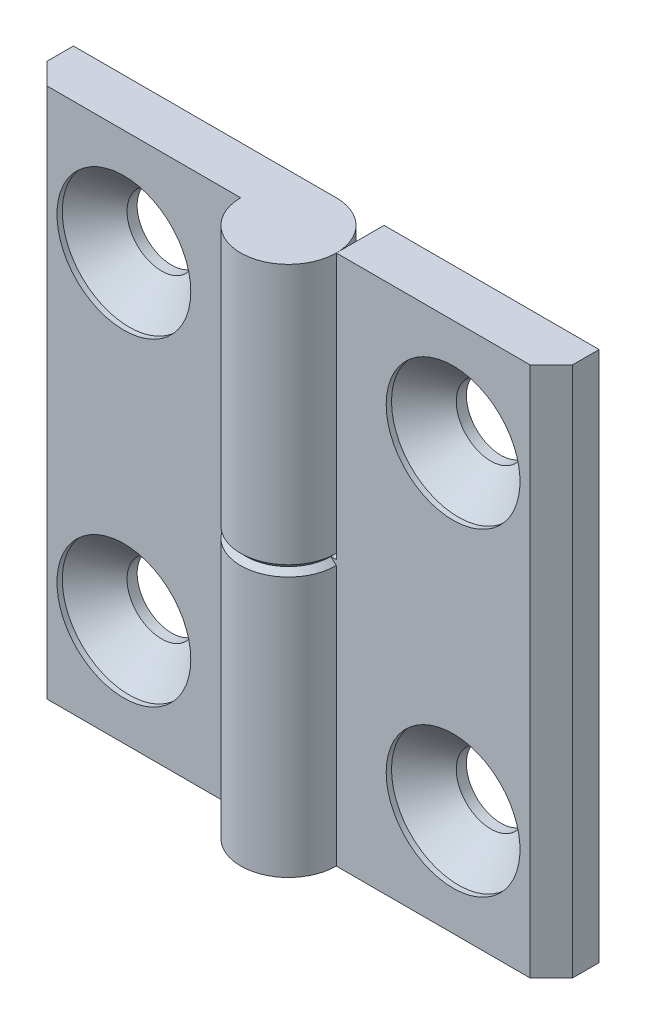
SolidWorks part; units mm, degrees
material "Алюминиевый сплав"
ref_plane "Спереди" through (0, 0, 0) normal (0, 0, 1) x (1, 0, 0)
ref_plane "Сверху" through (0, 0, 0) normal (0, 1, 0) x (1, 0, 0)
ref_plane "Справа" through (0, 0, 0) normal (1, 0, 0) x (0, 0, -1)
sketch "Эскиз1" plane through (0, 0, 0) normal (0, 1, 0) x (1, 0, 0)
  line L0 (0, 4.5) -> (-24.75, 4.5)
  line L1 (-24.75, 4.5) -> (-24.75, 2)
  line L2 (-24.75, 2) -> (-22.75, 0)
  line L3 (-22.75, 0) -> (-4.5, 0)
  line L4 (0, 0) -> (0, 10.5526) construction
  arc A0 (-4.5, 0) -> (0, 4.5) centre (0, 0) ccw
  dimension "D1" = 49.5
  dimension "D2" = 4.5
  dimension "D3" = 2.5
  dimension "D4" = 45
extrude "Бобышка-Вытянуть1" add sketch "Эскиз1" along normal mid plane 50
sketch "Эскиз3" plane through (0, 0, 0) normal (0, 0, 1) x (1, 0, 0)
  line L5 (-4.5, 25) -> (-4.5, -25) construction
  line L6 (4.5, -25) -> (-4.5, -25)
  line L7 (4.5, -25) -> (4.5, 0)
  line L8 (4.5, 0) -> (-4.5, 0)
  line L9 (-4.5, -25) -> (-4.5, 0)
extrude "Вырез-Вытянуть1" cut sketch "Эскиз3" against normal through all and the other way through all
hole_wizard "Зенковка для винта с полупотайной головкой M61" positions "Эскиз4" profile "Эскиз6" countersink size "M6" standard "ISO" end condition through all
sketch "Эскиз4" plane through (0, 0, 0) normal (0, 0, 1) x (1, 0, 0)
  line L0 (-15.5, 15) -> (-15.5, -15)
  line L2 (0, 0) -> (0, 18.9001) construction
  point P0 (-15.5, 15)
  point P2 (-15.5, -15)
  point P9 (-15.5, 0)
  dimension "D1" = 30
  dimension "D2" = 31
sketch "Эскиз6" plane through (-15.5, 15, 0) normal (1, 0, 0) x (0, -1, 0)
  line L0 (0, 0) -> (0, 4.5)
  line L1 (0, 4.5) -> (3.25, 4.5)
  line L2 (3.25, 4.5) -> (3.25, 3.55)
  line L3 (3.25, 3.55) -> (6.3, 0.5)
  line L4 (6.3, 0.5) -> (6.3, 0)
  line L6 (6.3, 0) -> (0, 0)
  line L7 (-3.25, 3.55) -> (-6.3, 0.5) construction
  line L11 (0, -6.35) -> (0, 107.95) construction
  dimension "Диаметр сквозного отверстия" = 6.5
  dimension "Глубина сквозного отверстия" = 4.5
  dimension "Диаметр зенковки" = 12.6
  dimension "Угол зенковки" = 90
  dimension "Утопленность" = 0.5
chamfer "Фаска1" distance 0.5 angle 45 2 edges at (-2.25, 0, -4.5) (3.182, 0, 3.182)
sketch "Угол раскрытия" plane through (0, 0, 0) normal (0, 1, 0) x (1, 0, 0)
  line L0 (0, 0) -> (0, -10)
  line L7 (0, 4.5) -> (-24.75, 4.5) construction
  dimension "D1" = 10
  dimension "D2" = 90
pattern_circular "Круговой массив1" count 2 over 360 about axis through (0, 0, 0) along (0, 0, 1) of bodies 106
